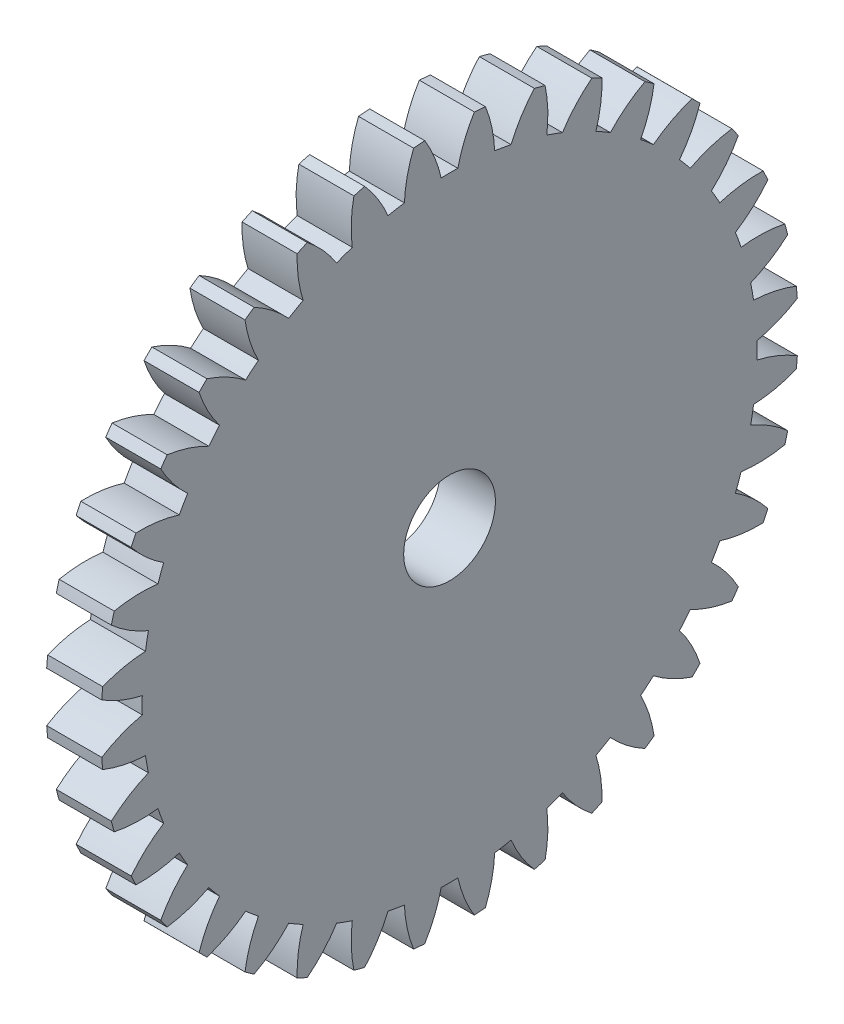
SolidWorks part; units mm, degrees
ref_plane "Plane1" through (0, 0, 0) normal (0, 0, 1) x (1, 0, 0)
ref_plane "Plane2" through (0, 0, 0) normal (0, 1, 0) x (1, 0, 0)
ref_plane "Plane3" through (0, 0, 0) normal (1, 0, 0) x (0, 0, -1)
sketch "HoldingSke" plane through (0, 0, 0) normal (0, 1, 0) x (1, 0, 0)
  line L0 (0, 0) -> (0.809, -0.5878)
  line L1 (-15, 0) -> (100, 0) construction
  line L2 (0, 0) -> (-2.1039, 2.3779)
  line L3 (0, 0) -> (-11.863, 4.5341)
  line L4 (0, 0) -> (6.9867, 5.0761)
  line L5 (0, 0) -> (-46.8476, -17.4728)
  line L6 (0, 0) -> (-2.4869, -1.6779)
  line L7 (-2.1039, 2.3779) -> (8.6586, 51.2059)
  line L8 (-76.2, 54.61) -> (-75.3, 54.61)
  line L9 (-71.009, 38.7566) -> (-53.1078, 45.2721)
  line L10 (-76.2, 71.12) -> (104.1128, 71.12)
  line L11 (0, 0) -> (-3, 0)
  line L12 (-76.2, 101.6) -> (-76.162, 101.6)
  line L13 (24.9733, 27.94) -> (52.9518, 28.4284)
  line L14 (24.9733, 27.94) -> (24.9743, 27.94)
  line L15 (24.9733, 27.94) -> (100.4006, 29.5858)
  line L16 (-63.627, -1) -> (-12.827, -1)
  circle A0 centre (0, 0) radius 2.5
  circle A1 centre (0, 0) radius 16.749
  circle A2 centre (0, 0) radius 37.5
  circle A3 centre (0, 0) radius 2.5
  dimension "MHD" = 33.498
  dimension "Hub_dia" = 75
  dimension "Bore" = 5
  dimension "MBD" = 5
  dimension "Num_teeth" = 36
  dimension "Pitch_radius" = 180.3128
  dimension "Pitch" = 1
  dimension "Width" = 3
  dimension "Overall_len" = 50
  dimension "Show_teeth" = 36
  dimension "Thickness" = 3
  dimension "OAL" = 50.0001
  dimension "T_dim" = 0.9
  dimension "Ap" = 20
  dimension "H" = 19.05
  dimension "Backlash" = 0.038
  dimension "Addendum_fac" = 1
  dimension "Dedendum_fac" = 1.25
  dimension "Clearance_fac" = 0.25
  dimension "Dedendum_add" = 0.001
  dimension "Module" = 1
sketch "BasProSke" plane through (0, 0, 0) normal (0, 1, 0) x (1, 0, 0)
  line L0 (-10, 0) -> (60, 0) construction
  line L1 (0, 0) -> (0, 19)
  line L2 (0, 0) -> (3, 0)
  line L3 (3, 0) -> (3, 19)
  line L4 (3, 19) -> (0, 19)
  dimension "Diameter" = 38
  dimension "Thickness" = 3
revolve "Base-Revolve" add sketch "BasProSke" angle 360 about L0
sketch "TooCutSke" plane through (0, 0, 0) normal (1, 0, 0) x (0, 0, -1)
  line L1 (0, 0) -> (0, 107) construction
  line L2 (0, 0) -> (-0.8516, 17.9798) construction
  line L3 (0, 0) -> (-3.1351, 35.8344) construction
  line L4 (-0.8516, 17.9798) -> (-1.5676, 17.9172) construction
  arc A0 (0.4547, 16.7428) -> (-0.4547, 16.7428) centre (0, 0) ccw
  arc A1 (1.3689, 18.9761) -> (-1.3689, 18.9761) centre (0, 0) ccw
  circle A2 centre (0, 0) radius 18 construction
  circle A3 centre (0, 0) radius 16.9145 construction
  arc A4 (-0.4547, 16.7428) -> (-1.3689, 18.9761) centre (-7.4808, 15.1702) ccw
  arc A5 (1.3689, 18.9761) -> (0.4547, 16.7428) centre (7.4808, 15.1702) ccw
  dimension "Root_dia" = 33.498
  dimension "Overcut_dia" = 38.0508
  dimension "Pitch_dia" = 36
  dimension "Base_dia" = 33.8289
  dimension "Flank_rad" = 7.2
  dimension "Half_ang" = 5
  dimension "Half_CT" = 0.7186
extrude "ToothCut" cut sketch "TooCutSke" along normal through all
fillet "Breaks" [suppressed] radius 0.02
fillet "RootFillets" [suppressed] radius 0.251
pattern_circular "TeethCuts" count 36 every 10 about axis through (-10, 0, 0) along (1, 0, 0) of "ToothCut", "RootFillets", "Breaks"
sketch "HubNeaOneSke" plane through (0, 0, 0) normal (-1, 0, 0) x (0, 0, 1)
  circle A0 centre (0, 0) radius 16.749
  dimension "Diameter" = 33.498
extrude "HubNearOne" [suppressed] add sketch "HubNeaOneSke" along normal blind 47.0001
sketch "HubNeaBotSke" plane through (0, 0, 0) normal (-1, 0, 0) x (0, 0, 1)
  circle A0 centre (0, 0) radius 16.749
  dimension "Diameter" = 33.498
extrude "HubNearBoth" [suppressed] add sketch "HubNeaBotSke" along normal blind 23.5
ref_plane "FarPln" through (3, 0, 0) normal (1, 0, 0) x (0, 0, -1)
sketch "HubFarSke" plane through (3, 0, 0) normal (1, 0, 0) x (0, 0, -1)
  circle A0 centre (0, 0) radius 16.749
  dimension "Diameter" = 33.498
extrude "HubFar" [suppressed] add sketch "HubFarSke" along normal blind 23.5
sketch "BorSke" plane through (0, 0, 0) normal (1, 0, 0) x (0, 0, -1)
  circle A0 centre (0, 0) radius 2.5
  dimension "Diameter" = 5
extrude "Bore" cut sketch "BorSke" along normal mid plane 100.0001
sketch "KeySke" plane through (0, 0, 0) normal (1, 0, 0) x (0, 0, -1)
  line L0 (-1, 0) -> (-1, 3.4)
  line L1 (-1, 3.4) -> (1, 3.4)
  line L2 (1, 3.4) -> (1, 0)
  line L3 (0, 0) -> (0, 34) construction
  line L4 (-1, 0) -> (1, 0)
  dimension "Offset" = 3.4
  dimension "Width" = 2
extrude "Keyway" [suppressed] cut sketch "KeySke" along normal mid plane 100.0001
pattern_circular "Keyway2" [suppressed] count 2 every 90 about axis through (-10, 0, 0) along (1, 0, 0)
equation "' \"Module@HoldingSke\" = 6.35"
equation "' \"Num_teeth@HoldingSke\" = 12"
equation "' \"Ap@HoldingSke\" =  20"
equation "' \"Width@HoldingSke\" = 0.5 * 25.4"
equation "' \"Hub_dia@HoldingSke\"= 1 * 25.4"
equation "' \"Overall_len@HoldingSke\" = 1.0 * 25.4"
equation "' \"Bore@HoldingSke\" = 0.75 * 25.4"
equation "' \"T_dim@HoldingSke\" = 0.1 * 25.4"
equation "' \"Width@KeySke\" = 0.25 * 25.4"
equation "' \"Show_teeth@HoldingSke\" = 13"
equation "' \"Backlash@HoldingSke\" = 0.009 * 25.4"
equation "' \"Addendum_fac@HoldingSke\" = 1.0"
equation "' \"Dedendum_fac@HoldingSke\" = 1.25"
equation "' \"Dedendum_add@HoldingSke\" = 0.00005 * 25.4"
equation "' \"Clearance_fac@HoldingSke\" = 0.25"
equation "\"Pitch@HoldingSke\" = 1 / \"Module@HoldingSke\""
equation "\"Overcut_dia@TooCutSke\" = (\"Num_teeth@HoldingSke\" + 2 * \"Addendum_fac@HoldingSke\") / \"Pitch@HoldingSke\" + 0.002 * 25.4"
equation "\"Pitch_dia@TooCutSke\" = \"Num_teeth@HoldingSke\" / \"Pitch@HoldingSke\""
equation "\"Base_dia@TooCutSke\" = \"Num_teeth@HoldingSke\" / \"Pitch@HoldingSke\" * cos((\"Ap@HoldingSke\"  * 3.14159265 / 180))"
equation "\"Root_dia@TooCutSke\" = (\"Num_teeth@HoldingSke\" + 2) / \"Pitch@HoldingSke\" - 2 * (\"Addendum_fac@HoldingSke\" + \"Dedendum_fac@HoldingSke\") / \"Pitch@HoldingSke\" - \"Dedendum_add@HoldingSke\" * 2"
equation "\"Half_ang@TooCutSke\" = 180 / \"Num_teeth@HoldingSke\""
equation "\"Half_CT@TooCutSke\" = \"Num_teeth@HoldingSke\" / \"Pitch@HoldingSke\" * sin((3.14159265 / 2 / \"Num_teeth@HoldingSke\")) / 2 - 7 * \"Backlash@HoldingSke\" / 4"
equation "\"Flank_rad@TooCutSke\" = \"Num_teeth@HoldingSke\" / \"Pitch@HoldingSke\" / 5"
equation "\"Radius@RootFillets\" = \"Clearance_fac@HoldingSke\" / \"Pitch@HoldingSke\" + \"Dedendum_add@HoldingSke\""
equation "\"Break_rad@Breaks\" = 0.02 / \"Pitch@HoldingSke\""
equation "\"Thickness@HoldingSke\" = \"Width@HoldingSke\""
equation "\"OAL@HoldingSke\" = \"Thickness@HoldingSke\""
equation "\"MHD@HoldingSke\" = (\"Num_teeth@HoldingSke\" + 2) / \"Pitch@HoldingSke\" - 2 * (\"Addendum_fac@HoldingSke\" + \"Dedendum_fac@HoldingSke\")  / \"Pitch@HoldingSke\" - \"Dedendum_add@HoldingSke\" * 2"
equation "\"MBD@HoldingSke\" = (\"Num_teeth@HoldingSke\" + 2) / \"Pitch@HoldingSke\" - 2 * (\"Addendum_fac@HoldingSke\" + \"Dedendum_fac@HoldingSke\")  / \"Pitch@HoldingSke\" - \"Dedendum_add@HoldingSke\" * 2 - 0.002 * 25.4"
equation "\"MHD@HoldingSke\" = ((sgn( \"MHD@HoldingSke\" - \"Hub_dia@HoldingSke\" )-1)*( \"MHD@HoldingSke\" - \"Hub_dia@HoldingSke\" ))/-2+ \"Hub_dia@HoldingSke\""
equation "\"MBD@HoldingSke\" = ((sgn( \"MBD@HoldingSke\" - \"Bore@HoldingSke\" )-1)*( \"MBD@HoldingSke\" - \"Bore@HoldingSke\" ))/-2+ \"Bore@HoldingSke\""
equation "\"OAL@HoldingSke\" = ((sgn( \"OAL@HoldingSke\" - \"Overall_len@HoldingSke\" )+1)*( \"OAL@HoldingSke\" - \"Overall_len@HoldingSke\" ))/2 + \"Overall_len@HoldingSke\" + 0.000002 * 25.4"
equation "\"Num_teeth@TeethCuts\" = int( \"Show_teeth@HoldingSke\" ) + 1"
equation "\"Num_teeth@TeethCuts\" = ((sgn( \"Num_teeth@TeethCuts\" - \"Num_teeth@HoldingSke\" )-1)*( \"Num_teeth@TeethCuts\" - \"Num_teeth@HoldingSke\" ))/-2+ \"Num_teeth@HoldingSke\""
equation "\"Num_teeth@TeethCuts\" = ((sgn( \"Num_teeth@TeethCuts\" - 2.0)+1)*( \"Num_teeth@TeethCuts\" - 2.0))/2 +2.0"
equation "\"Angle@TeethCuts\" = 360.0 / \"Num_teeth@HoldingSke\""
equation "\"Diameter@BasProSke\" = (\"Num_teeth@HoldingSke\" + 2 * \"Addendum_fac@HoldingSke\") / \"Pitch@HoldingSke\""
equation "\"Thickness@BasProSke\"  = \"Thickness@HoldingSke\""
equation "' \"Fillet_rad@BasProSke\" =  \"Thickness@HoldingSke\" * 0.05"
equation "\"MHD@HoldingSke\" = ((sgn( \"MHD@HoldingSke\" - \"Root_dia@TooCutSke\" )-1)*( \"MHD@HoldingSke\" - \"Root_dia@TooCutSke\" ))/-2+ \"Root_dia@TooCutSke\""
equation "\"Diameter@HubNeaOneSke\" = \"MHD@HoldingSke\""
equation "\"Length@HubNearOne\" = \"OAL@HoldingSke\" - \"Thickness@BasProSke\""
equation "\"Diameter@HubNeaBotSke\" = \"MHD@HoldingSke\""
equation "\"Length@HubNearBoth\" = ( \"OAL@HoldingSke\" - \"Thickness@BasProSke\" ) / 2.0"
equation "\"Thickness@FarPln\" = \"Thickness@BasProSke\""
equation "\"Diameter@HubFarSke\" = \"MHD@HoldingSke\""
equation "\"Length@HubFar\" = ( \"OAL@HoldingSke\" - \"Thickness@BasProSke\" ) / 2.0"
equation "\"Diameter@BorSke\" = \"MBD@HoldingSke\""
equation "\"D1@Bore\" = \"OAL@HoldingSke\" * 2.0"
equation "\"D1@Keyway\" = \"OAL@HoldingSke\" * 2.0"
equation "\"Offset@KeySke\" = \"T_dim@HoldingSke\" + \"MBD@HoldingSke\" / 2.0"
